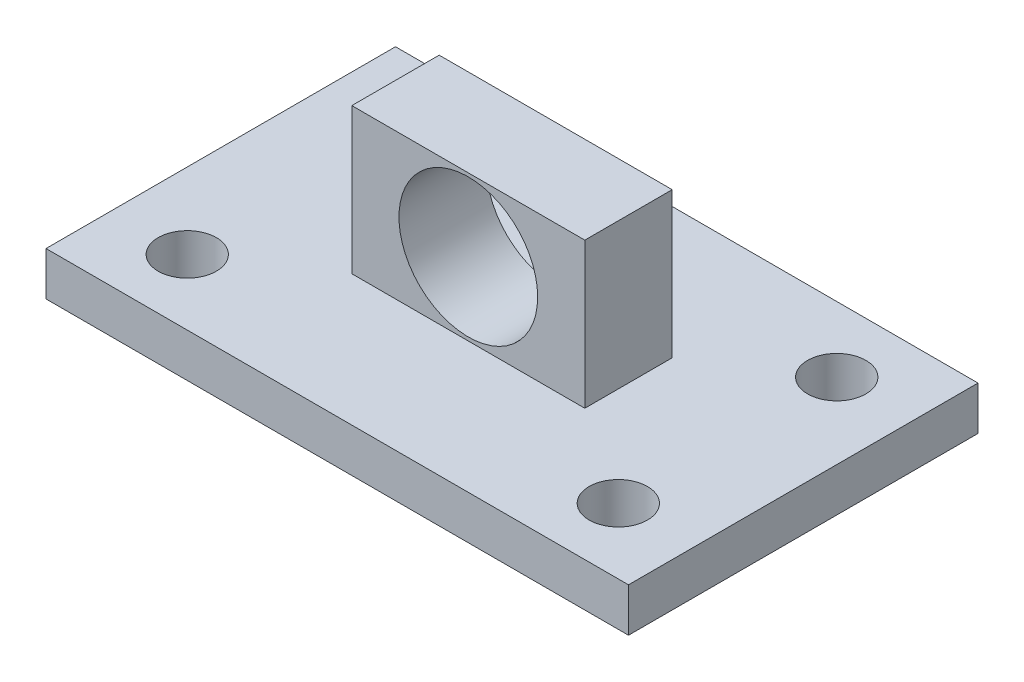
SolidWorks part; units mm, degrees
ref_plane "Front" through (0, 0, 0) normal (0, 0, 1) x (1, 0, 0)
ref_plane "Top" through (0, 0, 0) normal (0, 1, 0) x (1, 0, 0)
ref_plane "Right" through (0, 0, 0) normal (1, 0, 0) x (0, 0, -1)
sketch "草图1" plane through (0, 0, 0) normal (0, 1, 0) x (1, 0, 0)
  line L0 (0, 0) -> (0, 12) construction
  line L1 (0, 0) -> (20, 0) construction
  line L2 (-20, 12) -> (20, 12)
  line L3 (20, 12) -> (20, -12)
  line L4 (-20, 12) -> (-20, -12)
  line L5 (-20, -12) -> (20, -12)
  line L6 (0, 0) -> (0, -7.5) construction
  line L7 (0, -7.5) -> (-14.8, -7.5) construction
  circle A0 centre (-14.8, -7.5) radius 2
  circle A1 centre (14.8, -7.5) radius 2
  circle A2 centre (-14.8, 7.5) radius 2
  circle A3 centre (14.8, 7.5) radius 2
  point P9 (-20, 0)
extrude "凸台-拉伸1" add sketch "草图1" along normal blind 3
sketch "草图2" plane through (0, 3, 0) normal (0, 1, 0) x (1, 0, 0)
  line L0 (0, 0) -> (0, 3) construction
  line L1 (0, 3) -> (20, 3) construction
  line L2 (20, -12) -> (20, 12) construction
  line L3 (20, 3) -> (20, -3) construction
  line L10 (0, 0) -> (0, -3) construction
  line L11 (0, -3) -> (-8, -3) construction
  line L12 (-8, -3) -> (-8, 3) construction
  line L14 (-8, 3) -> (-8, -3)
  line L15 (-8, -3) -> (8, -3)
  line L17 (-8, 3) -> (8, 3)
  line L18 (8, 3) -> (8, -3)
extrude "凸台-拉伸2" add sketch "草图2" along normal blind 10
sketch "草图3" plane through (0, 0, 3) normal (0, 0, 1) x (1, 0, 0)
  line L0 (0, 3) -> (0, 8) construction
  line L1 (-20, 3) -> (20, 3) construction
  circle A0 centre (0, 8) radius 4.7625
extrude "切除-拉伸1" cut sketch "草图3" against normal blind 10
